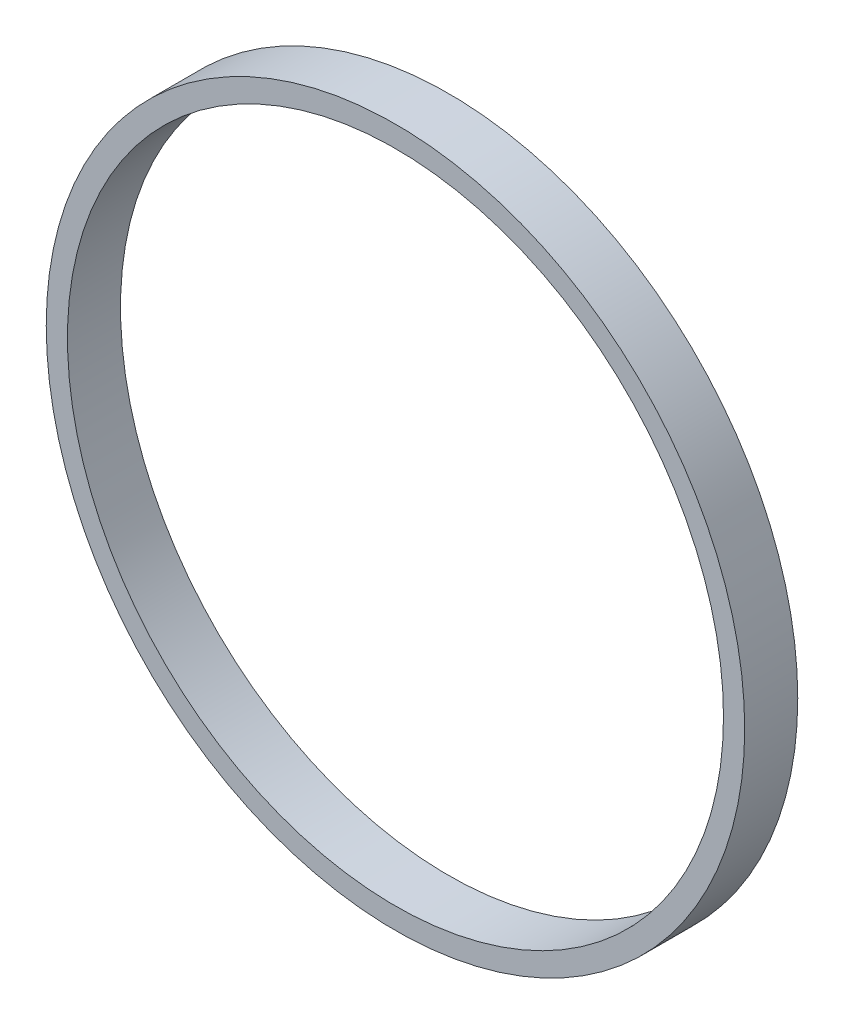
SolidWorks part; units mm, degrees
ref_plane "Front Plane" through (0, 0, 0) normal (0, 0, 1) x (1, 0, 0)
ref_plane "Top Plane" through (0, 0, 0) normal (0, 1, 0) x (1, 0, 0)
ref_plane "Right Plane" through (0, 0, 0) normal (1, 0, 0) x (0, 0, -1)
sketch "Sketch2" plane through (0, 0, 0) normal (0, 0, 1) x (1, 0, 0)
  circle A0 centre (0, 0) radius 39.2557
  circle A1 centre (0, 0) radius 41.7957
  dimension "D1" = 78.5114
  dimension "D2" = 2.54
extrude "Boss-Extrude1" add sketch "Sketch2" along normal blind 6.35
equation "\"AIRFRAME_OD\"= 3.091in"
equation "\"AIRFRAME_ID\"= 3.00in"
equation "\"FLAT_T\"= 0.125in"
equation "\"NOSE_EXP_L\"= 3.5in"
equation "\"NOSE_SHOULDER_L\"= 5in"
equation "\"MAIN_L\"= 30in"
equation "\"RECO_COUP_L\"= 6in"
equation "\"RECO_SWITCH_L\"= 1.5in"
equation "\"DROGUE_L\"= 14in"
equation "\"ATS_FORE_COUP_L\"= 4in"
equation "\"ATS_AFT_COUP_L\"= 2.5in"
equation "\"LOWER_L\"= 16in"
equation "\"FIN_N\"= 4"
equation "\"CR_AFT_X\"= 0.5in"
equation "\"CR_FORE_X\"= 6in"
equation "\"D1@Sketch2\"=\"AIRFRAME_OD\""
